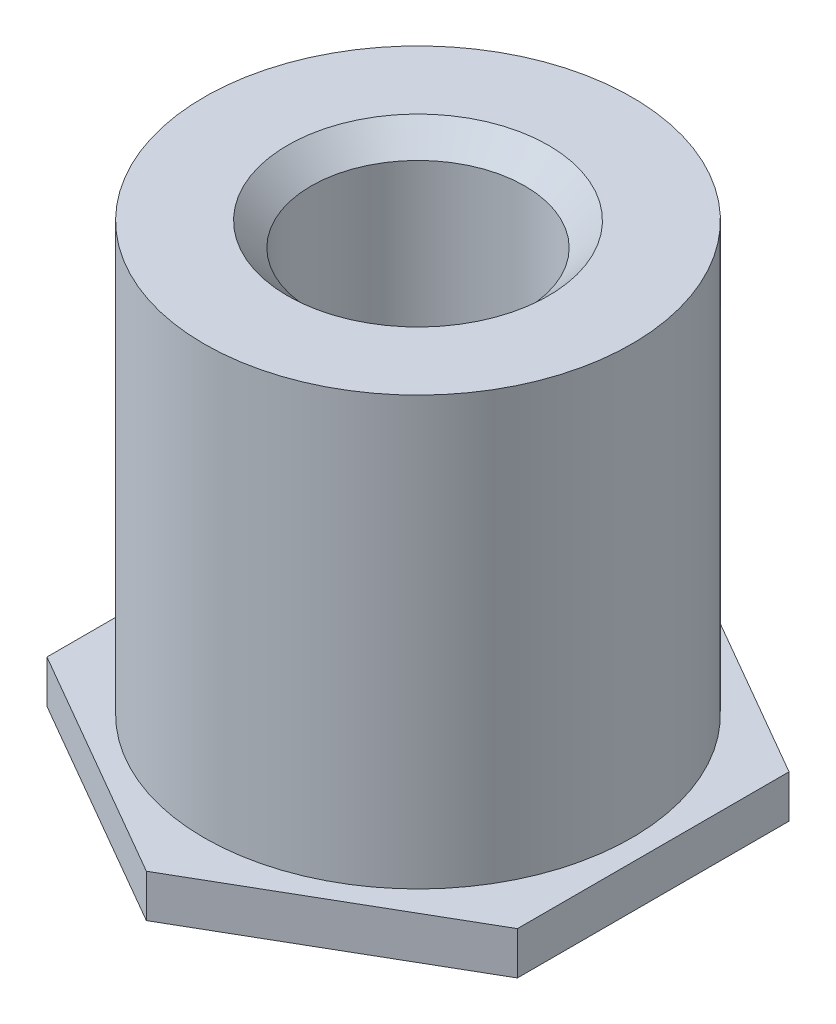
SolidWorks part; units mm, degrees
ref_plane "前视基准面" through (0, 0, 0) normal (0, 0, 1) x (1, 0, 0)
ref_plane "上视基准面" through (0, 0, 0) normal (0, 1, 0) x (1, 0, 0)
ref_plane "右视基准面" through (0, 0, 0) normal (1, 0, 0) x (0, 0, -1)
sketch "草图1" plane through (0, 0, 0) normal (0, 1, 0) x (1, 0, 0)
  line L0 (0, 0) -> (0, 3.1754) construction
  line L1 (0, -3.1754) -> (2.75, -1.5877)
  line L2 (2.75, -1.5877) -> (2.75, 1.5877)
  line L3 (2.75, 1.5877) -> (0, 3.1754)
  line L4 (0, 3.1754) -> (-2.75, 1.5877)
  line L5 (-2.75, 1.5877) -> (-2.75, -1.5877)
  line L6 (-2.75, -1.5877) -> (0, -3.1754)
  circle A0 centre (0, 0) radius 2.75 construction
  dimension "D1" = 5.5
extrude "凸台-拉伸1" add sketch "草图1" along normal blind 0.5
sketch "草图2" plane through (0, 0.5, 0) normal (0, 1, 0) x (1, 0, 0)
  circle A0 centre (0, 0) radius 2.5
  dimension "D1" = 5
extrude "凸台-拉伸2" add sketch "草图2" along normal blind 5
hole_wizard "M3 螺纹孔1" positions "草图3" profile "草图5" tap size "M3" standard "GB"
sketch "草图3" plane through (0, 5.5, 0) normal (0, 1, 0) x (1, 0, 0)
  point P0 (0, 0)
sketch "草图5" plane through (0, 5.5, 0) normal (1, 0, 0) x (0, 0, 1)
  line L0 (0, 0) -> (0, 4.7511)
  line L1 (0, 4.7511) -> (1.25, 4)
  line L2 (1.25, 4) -> (1.25, 0.275)
  line L3 (1.25, 0.275) -> (1.525, 0)
  line L5 (1.525, 0) -> (0, 0)
  line L6 (-1.25, 0.275) -> (-1.525, 0) construction
  line L10 (0, 4.7511) -> (-1.25, 4) construction
  line L11 (0, -6.35) -> (0, 107.95) construction
  dimension "螺纹孔钻头直径" = 2.5
  dimension "螺纹孔钻头深度" = 4
  dimension "近端锥形沉头孔直径" = 3.05
  dimension "近端锥形沉头孔角度" = 90
  dimension "导头角度" = 118
cosmetic thread "孔螺蚊线1" parameters "D1"=4, "D2"=3
